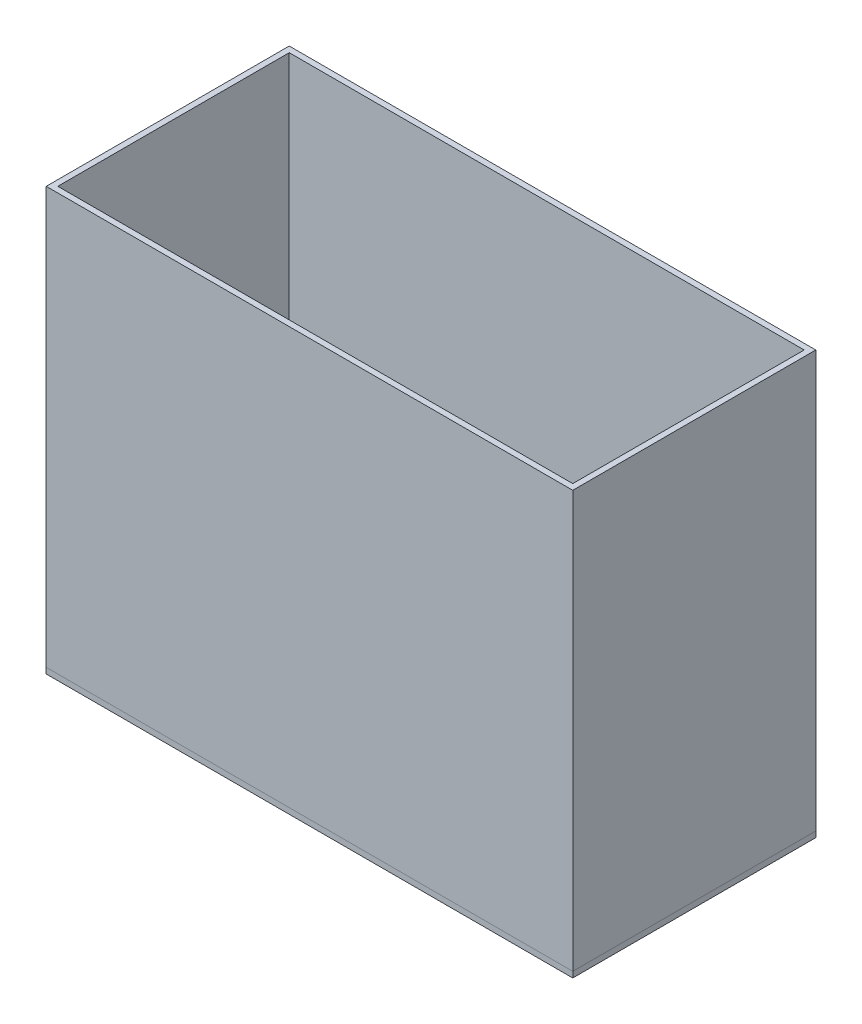
SolidWorks part; units mm, degrees
ref_plane "Front Plane" through (0, 0, 0) normal (0, 0, 1) x (1, 0, 0)
ref_plane "Top Plane" through (0, 0, 0) normal (0, 1, 0) x (1, 0, 0)
ref_plane "Right Plane" through (0, 0, 0) normal (1, 0, 0) x (0, 0, -1)
sketch "Sketch2" plane through (0, 0, 0) normal (0, 1, 0) x (1, 0, 0)
  line L1 (-230, 100) -> (225, 100)
  line L2 (-230, 100) -> (-230, -110)
  line L3 (-230, -110) -> (225, -110)
  line L4 (225, 100) -> (225, -110)
  line L5 (-225, 95) -> (220, 95)
  line L6 (-225, 95) -> (-225, -105)
  line L7 (-225, -105) -> (220, -105)
  line L8 (220, 95) -> (220, -105)
extrude "Boss-Extrude1" add sketch "Sketch2" along normal blind 360
sketch "Sketch3" plane through (0, 0, 0) normal (0, 1, 0) x (1, 0, 0)
  line L1 (-230, 100) -> (225, 100)
  line L2 (-230, 100) -> (-230, -110)
  line L3 (-230, -110) -> (225, -110)
  line L4 (225, 100) -> (225, -110)
extrude "Boss-Extrude4" add sketch "Sketch3" against normal blind 5 separate body
